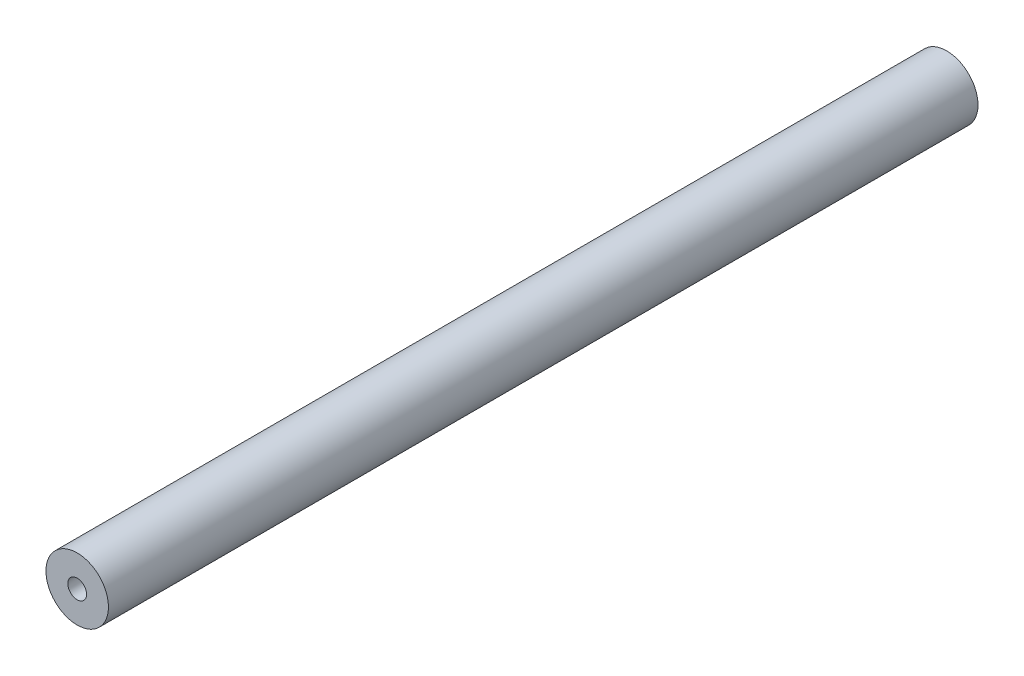
SolidWorks part; units mm, degrees
ref_plane "Front Plane" through (0, 0, 0) normal (0, 0, 1) x (1, 0, 0)
ref_plane "Top Plane" through (0, 0, 0) normal (0, 1, 0) x (1, 0, 0)
ref_plane "Right Plane" through (0, 0, 0) normal (1, 0, 0) x (0, 0, -1)
sketch "Sketch1" plane through (0, 0, 0) normal (0, 0, 1) x (1, 0, 0)
  circle A0 centre (0, 0) radius 31.75
  circle A1 centre (0, 0) radius 9.525
  dimension "D1" = 63.5
  dimension "D2" = 19.05
extrude "Boss-Extrude1" add sketch "Sketch1" along normal blind 883.412
